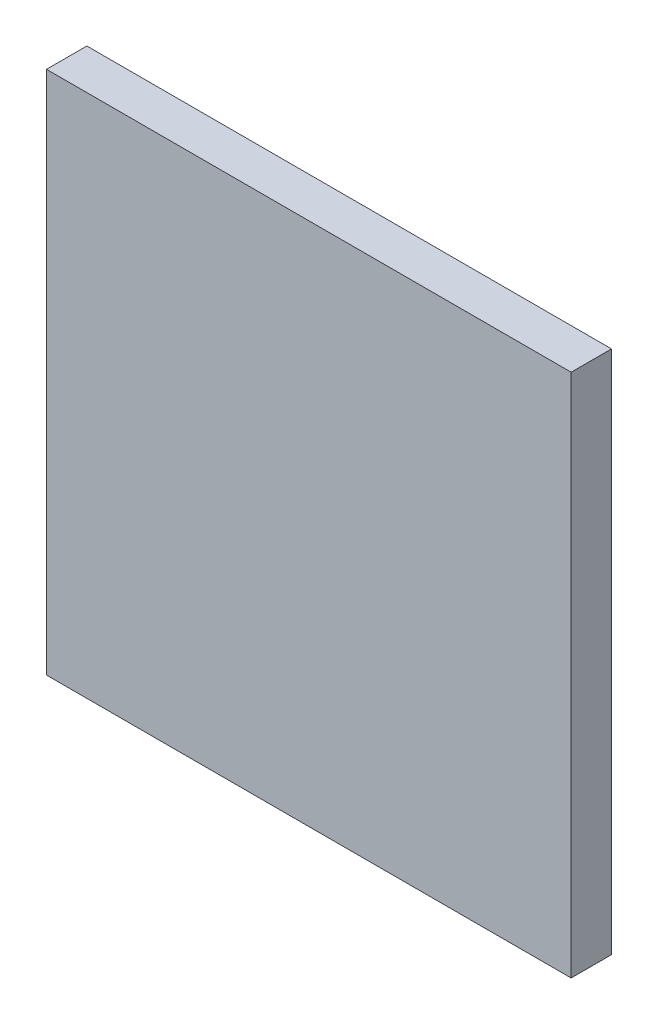
SolidWorks part; units mm, degrees
ref_plane "Front Plane" through (0, 0, 0) normal (0, 0, 1) x (1, 0, 0)
ref_plane "Top Plane" through (0, 0, 0) normal (0, 1, 0) x (1, 0, 0)
ref_plane "Right Plane" through (0, 0, 0) normal (1, 0, 0) x (0, 0, -1)
sketch "Sketch1" plane through (0, 0, 0) normal (0, 0, 1) x (1, 0, 0)
  line L1 (65, -65) -> (-65, -65)
  line L2 (65, -65) -> (65, 65)
  line L3 (65, 65) -> (-65, 65)
  line L4 (-65, -65) -> (-65, 65)
  line L5 (65, -65) -> (-65, 65) construction
  line L6 (65, 65) -> (-65, -65) construction
  point P0 (0, 0)
  dimension "D1" = 130
  dimension "D2" = 130
extrude "Boss-Extrude1" add sketch "Sketch1" along normal blind 10
